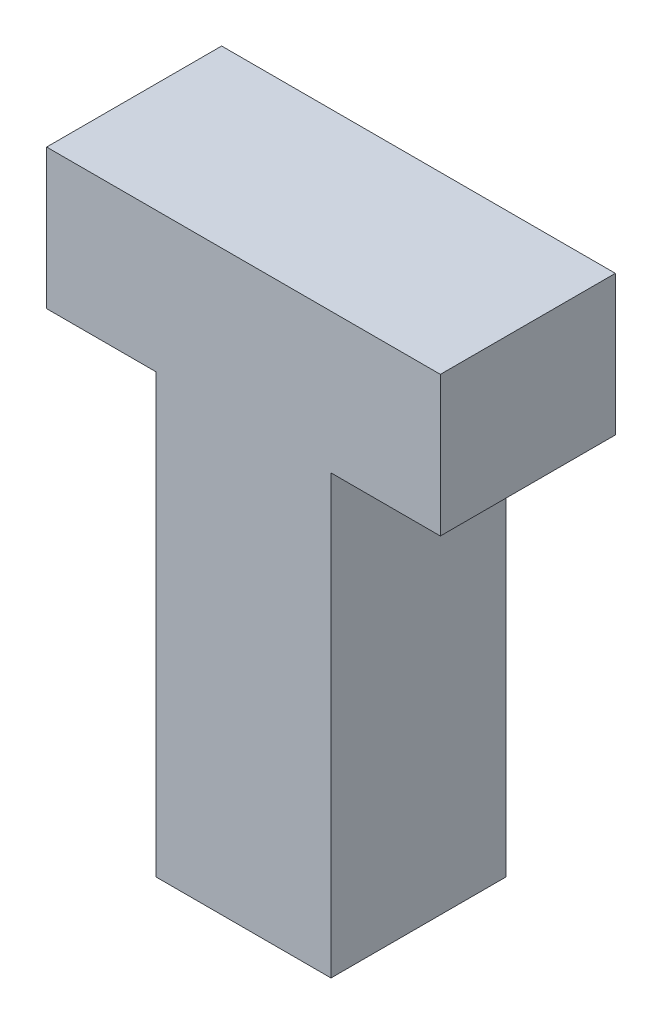
SolidWorks part; units mm, degrees
material "Медь"
ref_plane "Спереди" through (0, 0, 0) normal (0, 0, 1) x (1, 0, 0)
ref_plane "Сверху" through (0, 0, 0) normal (0, 1, 0) x (1, 0, 0)
ref_plane "Справа" through (0, 0, 0) normal (1, 0, 0) x (0, 0, -1)
sketch "Эскиз1" plane through (0, 0, 0) normal (0, 0, 1) x (1, 0, 0)
  line L0 (1, 0) -> (-1, 0)
  line L1 (-1, 0) -> (-1, 5)
  line L2 (-1, 5) -> (-2.25, 5)
  line L3 (-2.25, 5) -> (-2.25, 6.6)
  line L4 (-2.25, 6.6) -> (0, 6.6)
  line L7 (0, 6.6) -> (0, 0) construction
  line L9 (2.25, 6.6) -> (0, 6.6)
  line L10 (2.25, 5) -> (2.25, 6.6)
  line L11 (1, 5) -> (2.25, 5)
  line L12 (1, 0) -> (1, 5)
  dimension "D3" = 2.25
  dimension "D4" = 1.6
  dimension "D5" = 5
  dimension "D6" = 1
extrude "Бобышка-Вытянуть1" add sketch "Эскиз1" along normal mid plane 2
